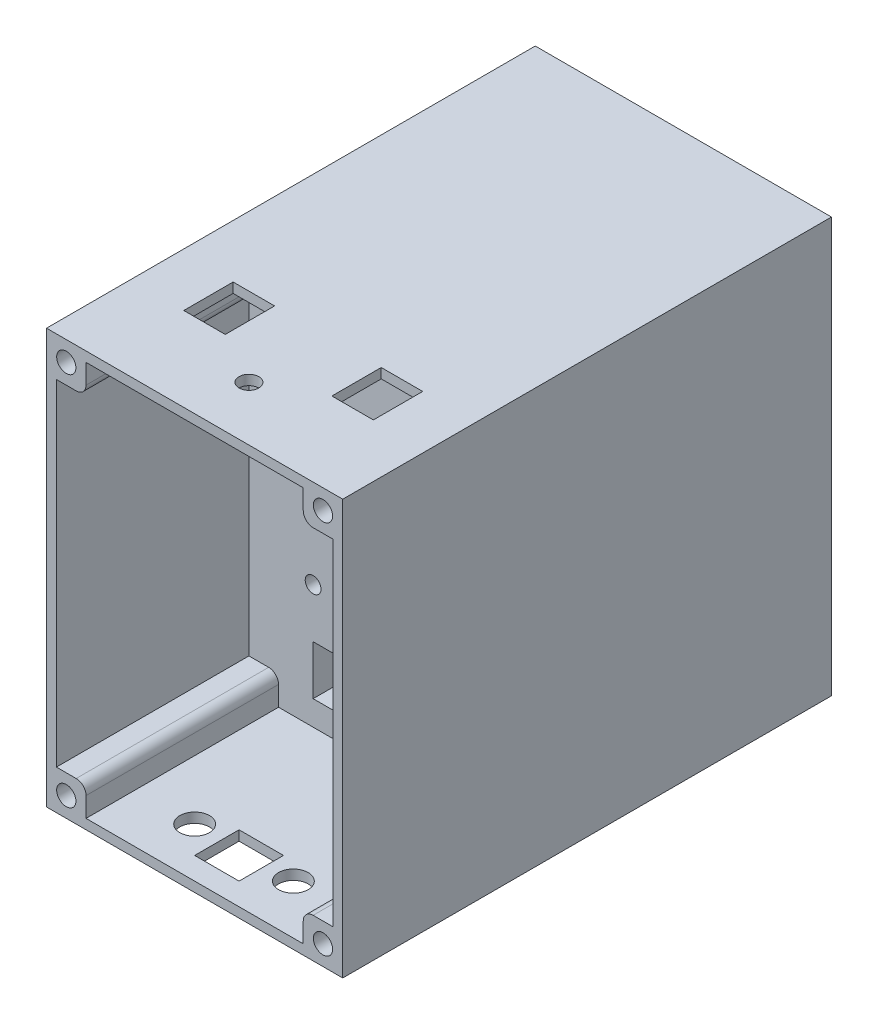
SolidWorks part; units mm, degrees
ref_plane "Front Plane" through (0, 0, 0) normal (0, 0, 1) x (1, 0, 0)
ref_plane "Top Plane" through (0, 0, 0) normal (0, 1, 0) x (1, 0, 0)
ref_plane "Right Plane" through (0, 0, 0) normal (1, 0, 0) x (0, 0, -1)
sketch "Sketch1" plane through (0, 0, 0) normal (0, 0, 1) x (1, 0, 0)
  line L1 (0, 0) -> (60, 0)
  line L2 (0, 0) -> (0, 84)
  line L3 (0, 84) -> (60, 84)
  line L4 (60, 0) -> (60, 84)
  dimension "D1" = 60
  dimension "D2" = 84
extrude "Boss-Extrude2" add sketch "Sketch1" along normal blind 82 and the other way blind 25
sketch "Sketch2" plane through (0, 0, 82) normal (0, 0, 1) x (1, 0, 0)
  line L14 (58, 82) -> (2, 82)
  line L15 (2, 2) -> (58, 2)
  line L16 (58, 82) -> (58, 2)
  line L17 (2, 82) -> (2, 2)
  dimension "D1" = 80
extrude "Cut-Extrude1" cut sketch "Sketch2" against normal through all
sketch "Sketch8" plane through (0, 0, -25) normal (0, 0, -1) x (-1, 0, 0)
  line L9 (-58, 82) -> (-52, 82)
  line L29 (-58, 82) -> (-2, 82) construction
  line L30 (-52, 82) -> (-52, 78)
  line L31 (-54, 76) -> (-58, 76)
  line L32 (-58, 2) -> (-58, 82) construction
  line L33 (-58, 76) -> (-58, 82)
  line L34 (-2, 2) -> (-8, 2)
  line L38 (-2, 76) -> (-2, 82)
  line L39 (-6, 76) -> (-2, 76)
  line L40 (-8, 82) -> (-8, 78)
  line L41 (-2, 82) -> (-8, 82)
  line L42 (-8, 2) -> (-8, 6)
  line L43 (-6, 8) -> (-2, 8)
  line L44 (-2, 8) -> (-2, 2)
  line L45 (-58, 8) -> (-58, 2)
  line L46 (-54, 8) -> (-58, 8)
  line L47 (-52, 2) -> (-52, 6)
  line L48 (-58, 2) -> (-52, 2)
  arc A5 (-52, 78) -> (-54, 76) centre (-54, 78) cw
  arc A6 (-8, 78) -> (-6, 76) centre (-6, 78) ccw
  arc A7 (-8, 6) -> (-6, 8) centre (-6, 6) cw
  arc A8 (-52, 6) -> (-54, 8) centre (-54, 6) ccw
  dimension "D1" = 2
extrude "Boss-Extrude6" add sketch "Sketch8" against normal up to surface (107 mm away) up to face at (30, 42, 82)
sketch "Sketch22" plane through (0, 0, -25) normal (0, 0, -1) x (-1, 0, 0)
  circle A4 centre (-56, 80) radius 1.95
  circle A5 centre (-4, 80) radius 1.95
  circle A6 centre (-4, 4) radius 1.95
  circle A7 centre (-56, 4) radius 1.95
extrude "Cut-Extrude6" cut sketch "Sketch22" against normal blind 25
sketch "Sketch26" plane through (0, 84, 0) normal (0, 1, 0) x (1, 0, 0)
  line L3 (15, -57) -> (10.8, -57)
  line L4 (15, -57) -> (19.2, -57)
  line L5 (10.8, -57) -> (10.8, -47)
  line L6 (10.8, -47) -> (19.2, -47)
  line L7 (19.2, -47) -> (19.2, -57)
  line L9 (40.8, -47) -> (40.8, -57)
  line L10 (49.2, -47) -> (40.8, -47)
  line L11 (49.2, -57) -> (49.2, -47)
  line L12 (45, -57) -> (40.8, -57)
  line L13 (45, -57) -> (49.2, -57)
extrude "Cut-Extrude9" cut sketch "Sketch26" against normal up to surface (2 mm away) up to face at (30, 82, 28.5)
sketch "Sketch28" plane through (0, 0, 0) normal (-1, 0, 0) x (0, 0, 1)
  line L0 (82, 84) -> (74, 84)
  line L2 (82, 84) -> (-25, 84) construction
  line L3 (74, 84) -> (74, -1.9465)
  line L4 (74, -1.9465) -> (82, -1.9465)
  line L5 (82, -1.9465) -> (82, 84)
extrude "Cut-Extrude11" cut sketch "Sketch28" against normal up to surface (60 mm away) up to face at (60, 42, 28.5)
sketch "Sketch32" plane through (0, 84, 0) normal (0, 1, 0) x (1, 0, 0)
  line L1 (60, -33) -> (60, -35)
  line L3 (0, 25) -> (0, -74) construction
  line L5 (60, 25) -> (60, -74) construction
  line L8 (60, -35) -> (0, -35)
  line L9 (0, -35) -> (0, -33)
  line L10 (0, -33) -> (0, -31)
  line L11 (0, -31) -> (60, -31)
  line L12 (60, -31) -> (60, -33)
extrude "Boss-Extrude9" add sketch "Sketch32" against normal up to surface (84 mm away) up to face at (30, 0, 24.5)
sketch "Sketch37" plane through (0, 0, 31) normal (0, 0, -1) x (-1, 0, 0)
  circle A0 centre (-15, 57) radius 1.6
  circle A1 centre (-45, 57) radius 1.6
  circle A2 centre (-45, 27) radius 1.6
  circle A3 centre (-15, 27) radius 1.6
extrude "Cut-Extrude15" cut sketch "Sketch37" against normal up to surface (4 mm away) up to face at (30, 42, 35)
sketch "Sketch38" plane through (0, 0, 31) normal (0, 0, -1) x (-1, 0, 0)
  line L8 (-30, 7) -> (-45, 7)
  line L9 (-45, 7) -> (-45, 17)
  line L10 (-45, 17) -> (-15, 17)
  line L11 (-15, 17) -> (-15, 7)
  line L12 (-15, 7) -> (-30, 7)
extrude "Cut-Extrude16" cut sketch "Sketch38" against normal up to surface (4 mm away) up to face at (16.6, 27, 35)
ref_plane "Plane1" through (0, 0, 24.5) normal (0, 0, -1) x (-1, 0, 0)
mirror "Mirror1" about plane through (0, 0, 24.5) normal (0, 0, -1) of "Cut-Extrude6"
sketch "Sketch41" plane through (0, 84, 0) normal (0, 1, 0) x (1, 0, 0)
  circle A0 centre (30, -63) radius 2
extrude "Cut-Extrude17" cut sketch "Sketch41" against normal up to surface (2 mm away) up to face at (15, 82, 52)
sketch "Sketch42" plane through (0, 0, 31) normal (0, 0, -1) x (-1, 0, 0)
  circle A0 centre (-30, 42) radius 11.5
extrude "Cut-Extrude18" cut sketch "Sketch42" against normal blind 2.5
sketch "Sketch43" plane through (0, 0, 33.5) normal (0, 0, -1) x (-1, 0, 0)
  circle A0 centre (-30, 42) radius 5
extrude "Cut-Extrude19" cut sketch "Sketch43" against normal up to surface (1.5 mm away) up to face at (30, 12, 35)
sketch "Sketch44" plane through (0, 0, 0) normal (0, -1, 0) x (1, 0, 0)
  line L4 (30, 69.5) -> (25.5, 69.5)
  line L5 (25.5, 69.5) -> (25.5, 60.5)
  line L6 (25.5, 60.5) -> (34.5, 60.5)
  line L7 (34.5, 60.5) -> (34.5, 69.5)
  line L8 (34.5, 69.5) -> (30, 69.5)
  circle A0 centre (20, 64) radius 3
  circle A2 centre (40, 64) radius 3
extrude "Cut-Extrude20" cut sketch "Sketch44" against normal up to surface (2 mm away) up to face at (30, 2, 54.5)
